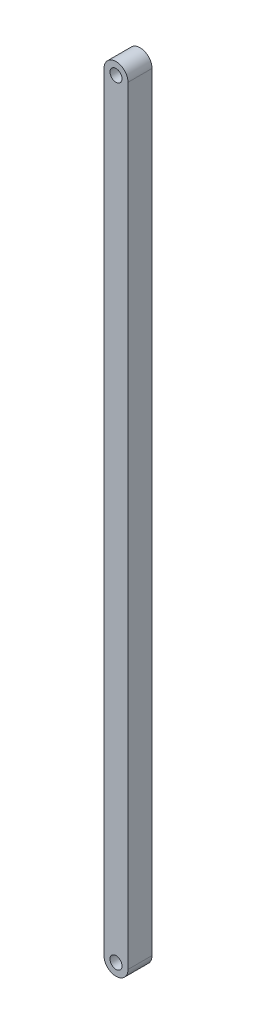
SolidWorks part; units mm, degrees
material "6061-T6 (SS)"
ref_plane "Plan de face" through (0, 0, 0) normal (0, 0, 1) x (1, 0, 0)
ref_plane "Plan de dessus" through (0, 0, 0) normal (0, 1, 0) x (1, 0, 0)
ref_plane "Plan de droite" through (0, 0, 0) normal (1, 0, 0) x (0, 0, -1)
sketch "Esquisse1" plane through (0, 0, 0) normal (0, 0, 1) x (1, 0, 0)
  line L2 (0, 0) -> (0, 406.4)
  line L4 (12.7, 0) -> (12.7, 406.4)
  arc A0 (12.7, 406.4) -> (0, 406.4) centre (6.35, 406.4) ccw
  arc A1 (0, 0) -> (12.7, 0) centre (6.35, 0) ccw
  circle A2 centre (6.35, 406.4) radius 3.175
  circle A3 centre (6.35, 0) radius 3.175
  dimension "D2" = 6.35
  dimension "D4" = 6.35
  dimension "D5" = 6.35
  dimension "D1" = 12.7
  dimension "D3" = 406.4
extrude "Boss.-Extru.1" add sketch "Esquisse1" along normal blind 12.7
